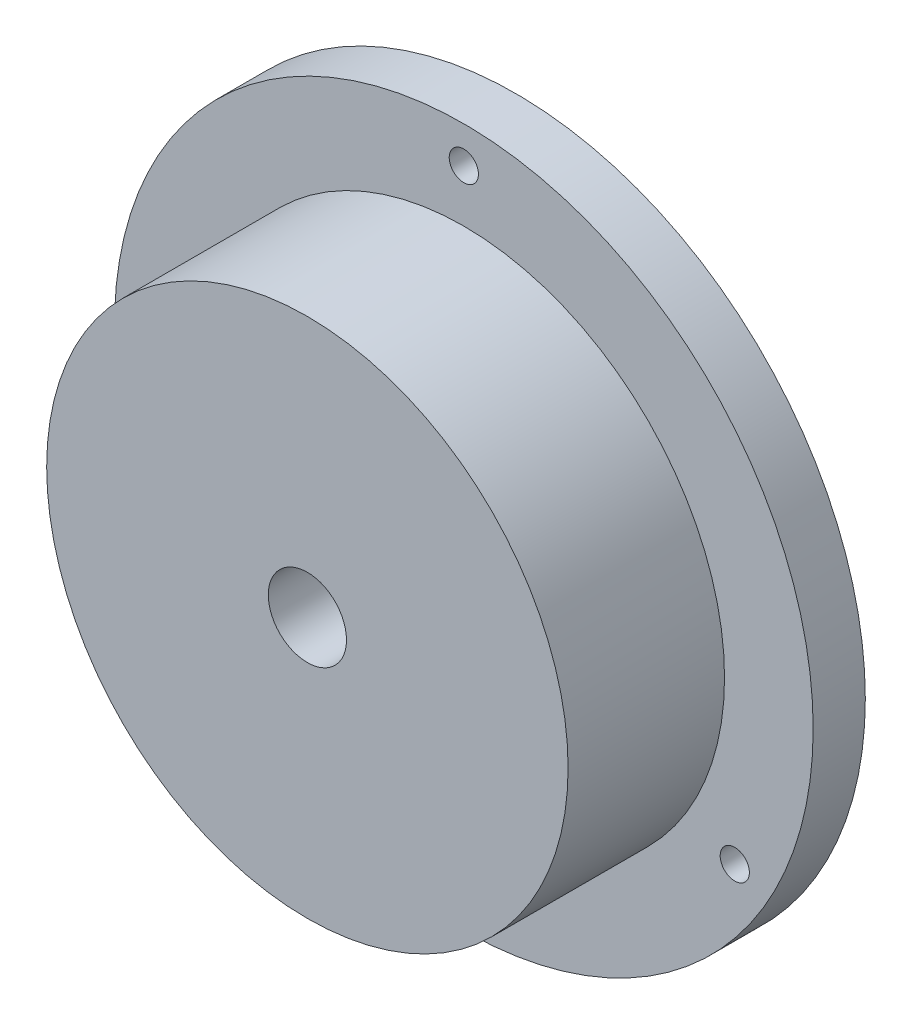
SolidWorks part; units mm, degrees
ref_plane "Front Plane" through (0, 0, 0) normal (0, 0, 1) x (1, 0, 0)
ref_plane "Top Plane" through (0, 0, 0) normal (0, 1, 0) x (1, 0, 0)
ref_plane "Right Plane" through (0, 0, 0) normal (1, 0, 0) x (0, 0, -1)
sketch "Sketch1" plane through (0, 0, 0) normal (0, 0, 1) x (1, 0, 0)
  circle A0 centre (0, 0) radius 21.2725
  dimension "D1" = 42.545
extrude "Boss-Extrude1" add sketch "Sketch1" along normal blind 3.175
sketch "Sketch2" plane through (0, 0, 3.175) normal (0, 0, 1) x (1, 0, 0)
  circle A0 centre (0, 0) radius 15.875
  dimension "D1" = 31.75
extrude "Boss-Extrude2" add sketch "Sketch2" along normal blind 9.525
hole_wizard "3/16 (0.1875) Diameter Hole1" positions "Sketch4" profile "Sketch3" hole size "3/16" standard "Ansi Inch" end condition through all
sketch "Sketch4" plane through (0, 0, 12.7) normal (0, 0, 1) x (1, 0, 0)
  point P1 (0, 0)
sketch "Sketch3" plane through (0, 0, 12.7) normal (1, 0, 0) x (0, -1, 0)
  line L0 (0, 0) -> (0, 12.7)
  line L1 (0, 12.7) -> (2.3812, 12.7)
  line L2 (2.3812, 12.7) -> (2.3812, 0)
  line L5 (2.3812, 0) -> (0, 0)
  line L11 (0, -6.35) -> (0, 107.95) construction
  dimension "Thru Hole Dia." = 4.7625
  dimension "Thru Hole Depth" = 12.7
hole_wizard "#2-56 Tapped Hole3" positions "Sketch10" profile "Sketch9" tap size "#2-56" standard "Ansi Inch" end condition through all
sketch "Sketch10" plane through (0, 0, 3.175) normal (0, 0, 1) x (1, 0, 0)
  point P1 (0, 19.05)
  dimension "D1" = 19.05
sketch "Sketch9" plane through (0, 19.05, 3.175) normal (1, 0, 0) x (0, -1, 0)
  line L0 (0, 0) -> (0, 3.175)
  line L1 (0, 3.175) -> (0.889, 3.175)
  line L2 (0.889, 3.175) -> (0.889, 0)
  line L5 (0.889, 0) -> (0, 0)
  line L11 (0, -6.35) -> (0, 107.95) construction
  dimension "Thread Major Dia." = 1.778
  dimension "Thru Tap Drill Depth" = 3.175
pattern_circular "CirPattern1" count 3 every 120 about axis through (0, 0, 0) along (0, 0, 1) of "#2-56 Tapped Hole3"
sketch "Sketch11" plane through (0, 0, 0) normal (0, 0, -1) x (-1, 0, 0)
  line L0 (0, 0) -> (0, -21.2725) construction
  circle A1 centre (0, 0) radius 21.2725 construction
ref_plane "Plane1" through (0, -21.2725, 0) normal (0, -1, 0) x (1, 0, 0)
hole_wizard "#8-32 Tapped Hole1" positions "Sketch13" profile "Sketch12" tap size "#8-32" standard "Ansi Inch"
sketch "Sketch13" plane through (0, -21.2725, 0) normal (0, -1, 0) x (1, 0, 0)
  line L0 (-21.2725, 0) -> (21.2725, 0) construction
  point P1 (0, 7.9248)
  dimension "D1" = 7.9248
sketch "Sketch12" plane through (0, -21.2725, 7.9248) normal (1, 0, 0) x (0, 0, -1)
  line L0 (0, 0) -> (0, 22.3093)
  line L1 (0, 22.3093) -> (1.7272, 21.2715)
  line L2 (1.7272, 21.2715) -> (1.7272, 0)
  line L5 (1.7272, 0) -> (0, 0)
  line L10 (0, 22.3093) -> (-1.7272, 21.2715) construction
  line L11 (0, -6.35) -> (0, 107.95) construction
  dimension "Tap Drill Dia." = 3.4544
  dimension "Tap Drill Depth" = 21.2715
  dimension "Drill Angle" = 118
